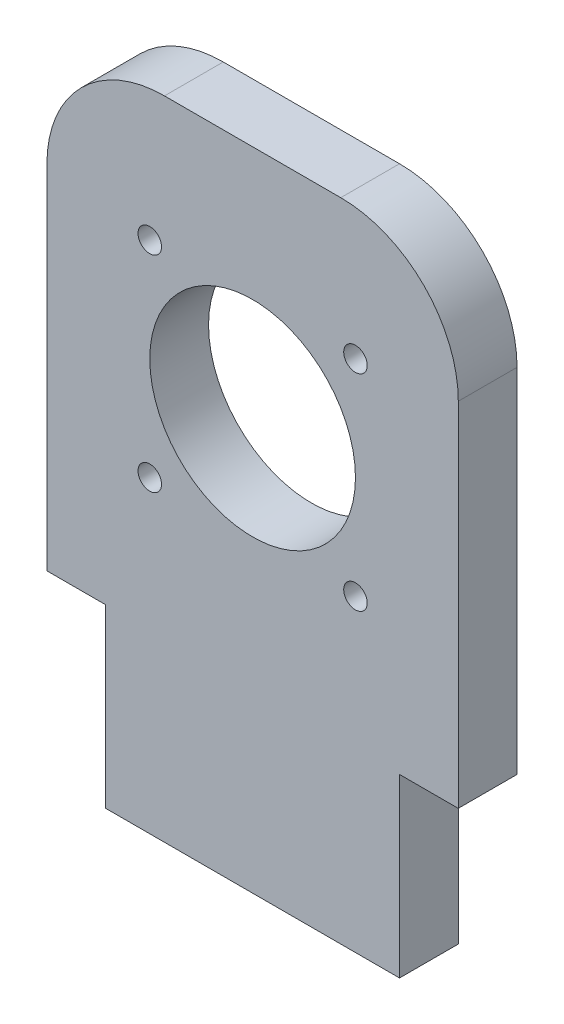
SolidWorks part; units mm, degrees
material "6061-T6 (SS)"
ref_plane "Front Plane" through (0, 0, 0) normal (0, 0, 1) x (1, 0, 0)
ref_plane "Top Plane" through (0, 0, 0) normal (0, 1, 0) x (1, 0, 0)
ref_plane "Right Plane" through (0, 0, 0) normal (1, 0, 0) x (0, 0, -1)
sketch "Sketch1" plane through (0, 0, 0) normal (0, 0, 1) x (1, 0, 0)
  line L0 (0, 0) -> (70, 0)
  line L1 (0, 0) -> (0, -80)
  line L2 (70, 0) -> (70, -80)
  line L3 (0, -80) -> (70, -80)
  line L4 (10, -80) -> (60, -80)
  line L5 (10, -80) -> (10, -110)
  line L6 (60, -80) -> (60, -110)
  line L7 (10, -110) -> (60, -110)
  circle A0 centre (35, -40) radius 17.5
  point P7 (35, -80)
  point P8 (35, 0)
  point P11 (35, -80)
  dimension "D3" = 35
  dimension "D1" = 70
  dimension "D2" = 80
  dimension "D4" = 40
  dimension "D5" = 50
  dimension "D6" = 30
extrude "Boss-Extrude1" add sketch "Sketch1" along normal blind 10 contours L5 L7 L6 L3 | A0
fillet "Fillet1" radius 20 2 edges at (70, 0, 5) (0, 0, 5)
sketch "Sketch2" plane through (0, 0, 10) normal (0, 0, 1) x (1, 0, 0)
  line L1 (17.5, -57.5) -> (52.5, -57.5) construction
  line L2 (17.5, -57.5) -> (17.5, -22.5) construction
  line L3 (17.5, -22.5) -> (52.5, -22.5) construction
  line L4 (52.5, -57.5) -> (52.5, -22.5) construction
  line L5 (17.5, -57.5) -> (52.5, -22.5) construction
  line L6 (17.5, -22.5) -> (52.5, -57.5) construction
  circle A0 centre (17.5, -22.5) radius 2
  circle A1 centre (52.5, -22.5) radius 2
  circle A2 centre (52.5, -57.5) radius 2
  circle A3 centre (17.5, -57.5) radius 2
  point P0 (35, -40)
  dimension "D2" = 4
  dimension "D1" = 35
extrude "Cut-Extrude1" cut sketch "Sketch2" against normal blind 10
